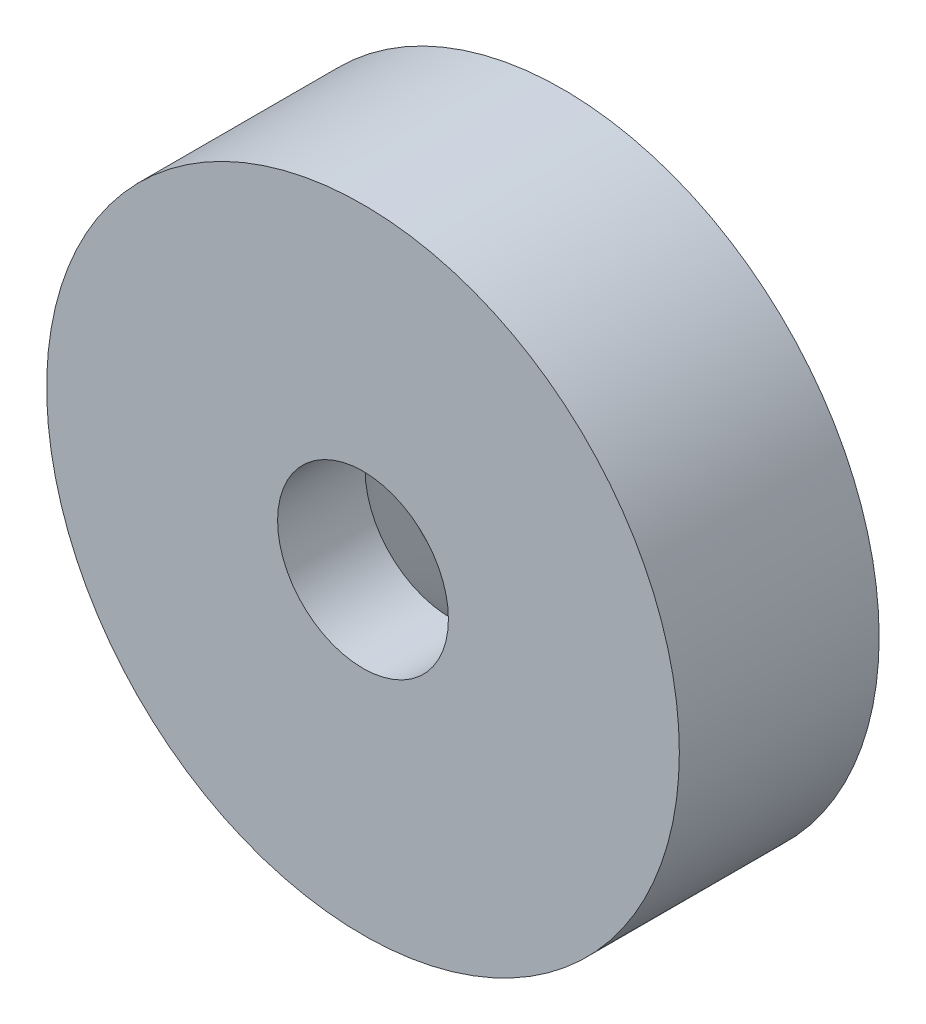
SolidWorks part; units mm, degrees
ref_plane "Front Plane" through (0, 0, 0) normal (0, 0, 1) x (1, 0, 0)
ref_plane "Top Plane" through (0, 0, 0) normal (0, 1, 0) x (1, 0, 0)
ref_plane "Right Plane" through (0, 0, 0) normal (1, 0, 0) x (0, 0, -1)
sketch "Sketch1" plane through (0, 0, 0) normal (0, 0, 1) x (1, 0, 0)
  circle A0 centre (5.0563, 23.079) radius 6
  circle A1 centre (5.0563, 23.079) radius 1.62
extrude "Boss-Extrude1" add sketch "Sketch1" along normal blind 3.79
sketch "Sketch2" plane through (0, 0, 0) normal (0, 0, -1) x (-1, 0, 0)
  circle A0 centre (-5.0563, 23.079) radius 3.75
  dimension "D1" = 7.5
extrude "Cut-Extrude1" cut sketch "Sketch2" against normal blind 10 draft 45
